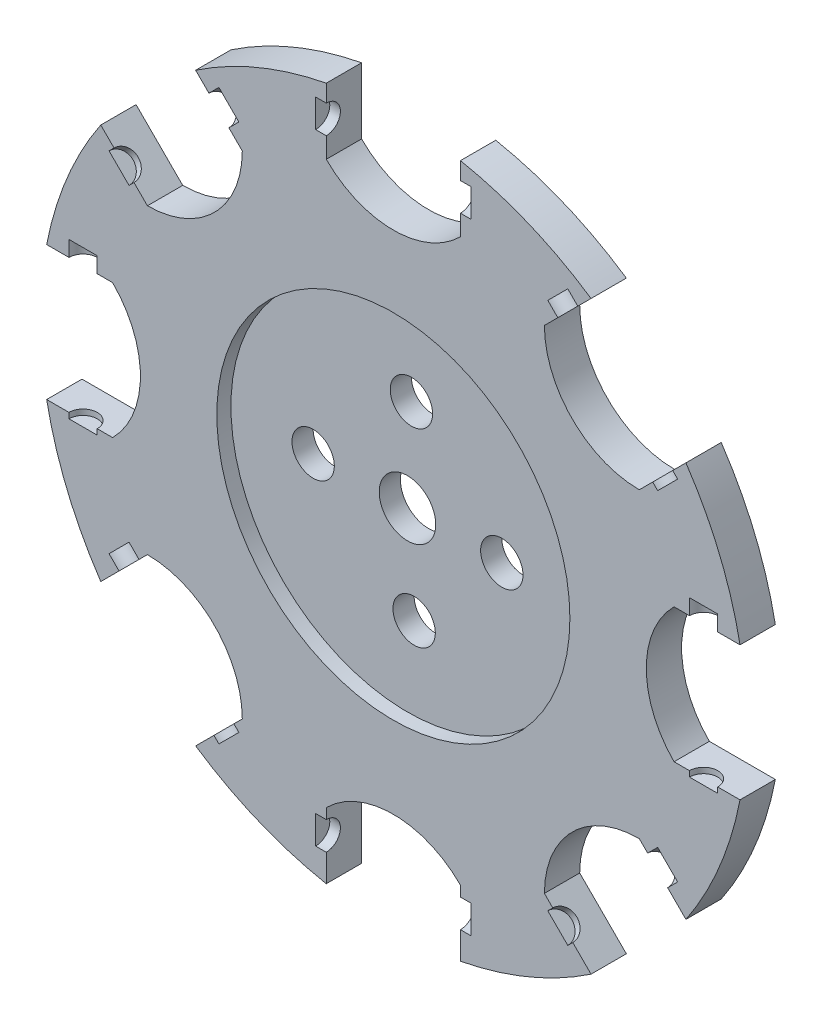
SolidWorks part; units mm, degrees
other "Markup1"
sketch "Sketch5" plane through (-91.0488, -42.4081, 2.54) normal (0, 0, 1) x (1, 0, 0)
ref_plane "Front Plane" through (0, 0, 0) normal (0, 0, 1) x (1, 0, 0)
ref_plane "Top Plane" through (0, 0, 0) normal (0, 1, 0) x (1, 0, 0)
ref_plane "Right Plane" through (0, 0, 0) normal (1, 0, 0) x (0, 0, -1)
sketch "Sketch6" plane through (0, 0, 0) normal (0, 0, 1) x (1, 0, 0)
  line L1 (40.1881, 1463.4992) -> (40.1881, 1226.2446)
  line L2 (522.7881, 1463.4992) -> (522.7881, 1226.2446)
  line L3 (281.4881, 216.6334) -> (-628.1733, 216.6334) construction
  line L4 (992.5305, 1268.9256) -> (824.7661, 1101.1612)
  line L5 (1333.7802, 927.6758) -> (1166.0159, 759.9115)
  line L6 (1528.3539, 457.9334) -> (1291.0993, 457.9334)
  line L7 (1528.3539, -24.6666) -> (1291.0993, -24.6666)
  line L8 (1333.7802, -494.409) -> (1166.0159, -326.6446)
  line L9 (992.5305, -835.6587) -> (824.7661, -667.8943)
  line L10 (522.7881, -1030.2324) -> (522.7881, -792.9777)
  line L11 (40.1881, -1030.2324) -> (40.1881, -792.9777)
  line L12 (-429.5543, -835.6587) -> (-261.7899, -667.8943)
  line L13 (-770.804, -494.409) -> (-603.0397, -326.6446)
  line L14 (-965.3777, -24.6666) -> (-728.1231, -24.6666)
  line L15 (-965.3777, 457.9334) -> (-728.1231, 457.9334)
  line L16 (-770.804, 927.6758) -> (-603.0397, 759.9115)
  line L17 (-429.5543, 1268.9256) -> (-261.7899, 1101.1612)
  arc A0 (40.1881, 1463.4992) -> (-429.5543, 1268.9256) centre (281.4881, 216.6334) ccw
  arc A1 (40.1881, 1226.2446) -> (522.7881, 1226.2446) centre (281.4881, 1467.5446) ccw
  arc A3 (824.7661, 1101.1612) -> (1166.0159, 759.9115) centre (1166.0159, 1101.1612) ccw
  arc A4 (1291.0993, 457.9334) -> (1291.0993, -24.6666) centre (1532.3993, 216.6334) ccw
  arc A5 (1166.0159, -326.6446) -> (824.7661, -667.8943) centre (1166.0159, -667.8943) ccw
  arc A6 (522.7881, -792.9777) -> (40.1881, -792.9777) centre (281.4881, -1034.2777) ccw
  arc A7 (-261.7899, -667.8943) -> (-603.0397, -326.6446) centre (-603.0397, -667.8943) ccw
  arc A8 (-728.1231, -24.6666) -> (-728.1231, 457.9334) centre (-969.4231, 216.6334) ccw
  arc A9 (-603.0397, 759.9115) -> (-261.7899, 1101.1612) centre (-603.0397, 1101.1612) ccw
  arc A10 (-770.804, 927.6758) -> (-965.3777, 457.9334) centre (281.4881, 216.6334) ccw
  arc A11 (992.5305, 1268.9256) -> (522.7881, 1463.4992) centre (281.4881, 216.6334) ccw
  arc A12 (-965.3777, -24.6666) -> (-770.804, -494.409) centre (281.4881, 216.6334) ccw
  arc A13 (1528.3539, 457.9334) -> (1333.7802, 927.6758) centre (281.4881, 216.6334) ccw
  arc A14 (1333.7802, -494.409) -> (1528.3539, -24.6666) centre (281.4881, 216.6334) ccw
  arc A15 (522.7881, -1030.2324) -> (992.5305, -835.6587) centre (281.4881, 216.6334) ccw
  arc A16 (-429.5543, -835.6587) -> (40.1881, -1030.2324) centre (281.4881, 216.6334) ccw
  point P49 (281.4881, 216.6334)
  dimension "D1" = 2540
  dimension "D3" = 8
extrude "Boss-Extrude3" add sketch "Sketch6" along normal blind 127
sketch "Sketch8" plane through (0, 0, 127) normal (0, 0, 1) x (1, 0, 0)
  line L0 (-631.9367, 221.5025) -> (1583.6915, 253.4683) construction
  line L1 (281.4881, 1126.2949) -> (281.4881, -1783.7728) construction
  arc A0 (40.1881, 1226.2446) -> (522.7881, 1226.2446) centre (281.4881, 1467.5446) ccw construction
  circle A1 centre (281.4881, 234.6809) radius 339.284
  circle A2 centre (295.6976, 573.6672) radius 76.2
  circle A3 centre (305.4711, -103.7544) radius 76.2
  circle A4 centre (-57.7959, 234.6809) radius 76.2
  circle A5 centre (620.7721, 234.6809) radius 76.2
  circle A6 centre (281.4881, 234.6809) radius 101.6
extrude "Cut-Extrude1" cut sketch "Sketch8" against normal blind 127 contours A1 A2 | A1 A2 | A5 A1 | A5 A1 | A3 A1 | A3 A1 | A1 A4 | A1 A4 | A6
sketch "Sketch9" plane through (0, 0, 127) normal (0, 0, 1) x (1, 0, 0)
  circle A0 centre (281.4881, 234.6809) radius 635
extrude "Cut-Extrude2" cut sketch "Sketch9" against normal blind 50.8
sketch "Sketch11" plane through (0, 0, 127) normal (0, 0, 1) x (1, 0, 0)
  line L0 (281.4881, 1126.2949) -> (281.4881, 1491.9489) construction
  line L1 (560.8881, 1350.5311) -> (2.0881, 1350.5311)
  line L2 (2.0881, 1350.5311) -> (2.0881, 1401.3311)
  line L3 (2.0881, 1401.3311) -> (560.8881, 1401.3311)
  line L4 (560.8881, 1401.3311) -> (560.8881, 1350.5311)
  arc A0 (40.1881, 1226.2446) -> (522.7881, 1226.2446) centre (281.4881, 1467.5446) ccw construction
  point P9 (281.4881, 1350.5311)
revolve "Cut-Revolve1" cut sketch "Sketch11" angle 360 about L1
pattern_circular "CirPattern1" count 8 over 360 about axis through (281.4881, 234.6809, 0) along (0, 0, 1) of "Cut-Revolve1"
